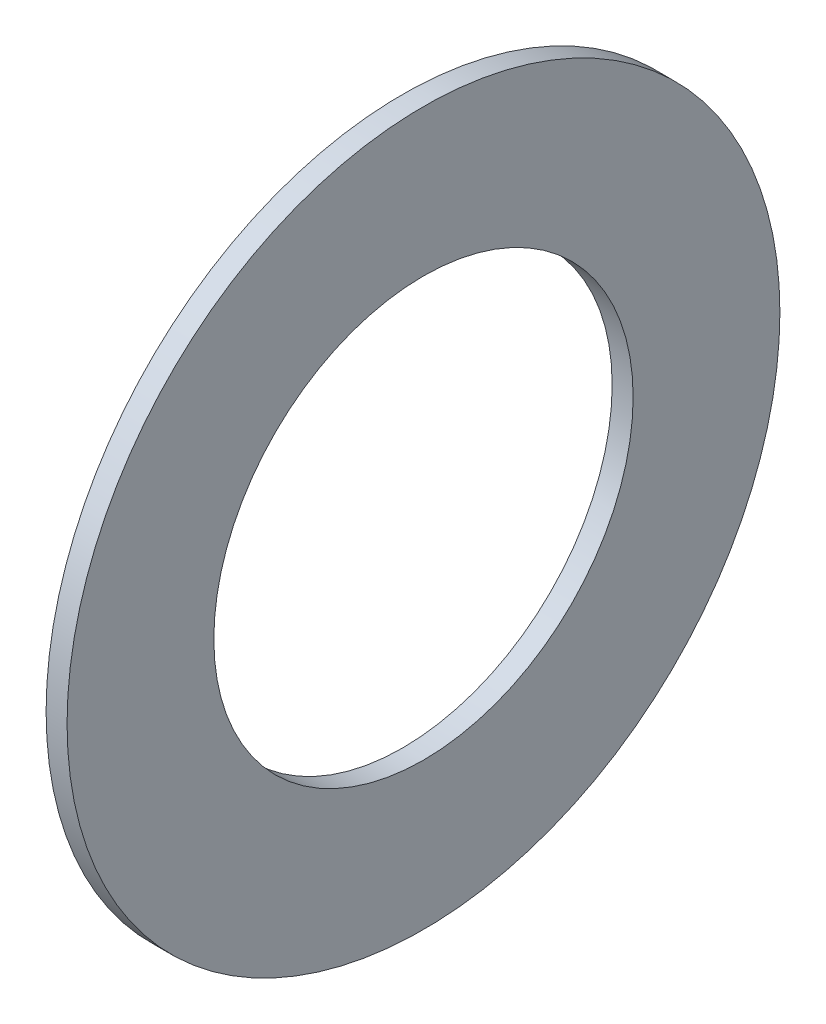
SolidWorks part; units mm, degrees
ref_plane "Front Plane" through (0, 0, 0) normal (0, 0, 1) x (1, 0, 0)
ref_plane "Top Plane" through (0, 0, 0) normal (0, 1, 0) x (1, 0, 0)
ref_plane "Right Plane" through (0, 0, 0) normal (1, 0, 0) x (0, 0, -1)
ref_plane "Plane1" through (0, 0, 0) normal (0, 0, 1) x (1, 0, 0)
sketch "Sketch1" plane through (0, 0, 0) normal (0, 0, 1) x (1, 0, 0)
  line L0 (-2, 10) -> (-1, 10)
  line L1 (-1, 10) -> (-1, 17)
  line L2 (-1, 17) -> (-2, 17)
  line L3 (-2, 17) -> (-2, 10)
  line L4 (50, 0) -> (-50, 0) construction
revolve "Revolve1" add sketch "Sketch1" angle 360 about L4
